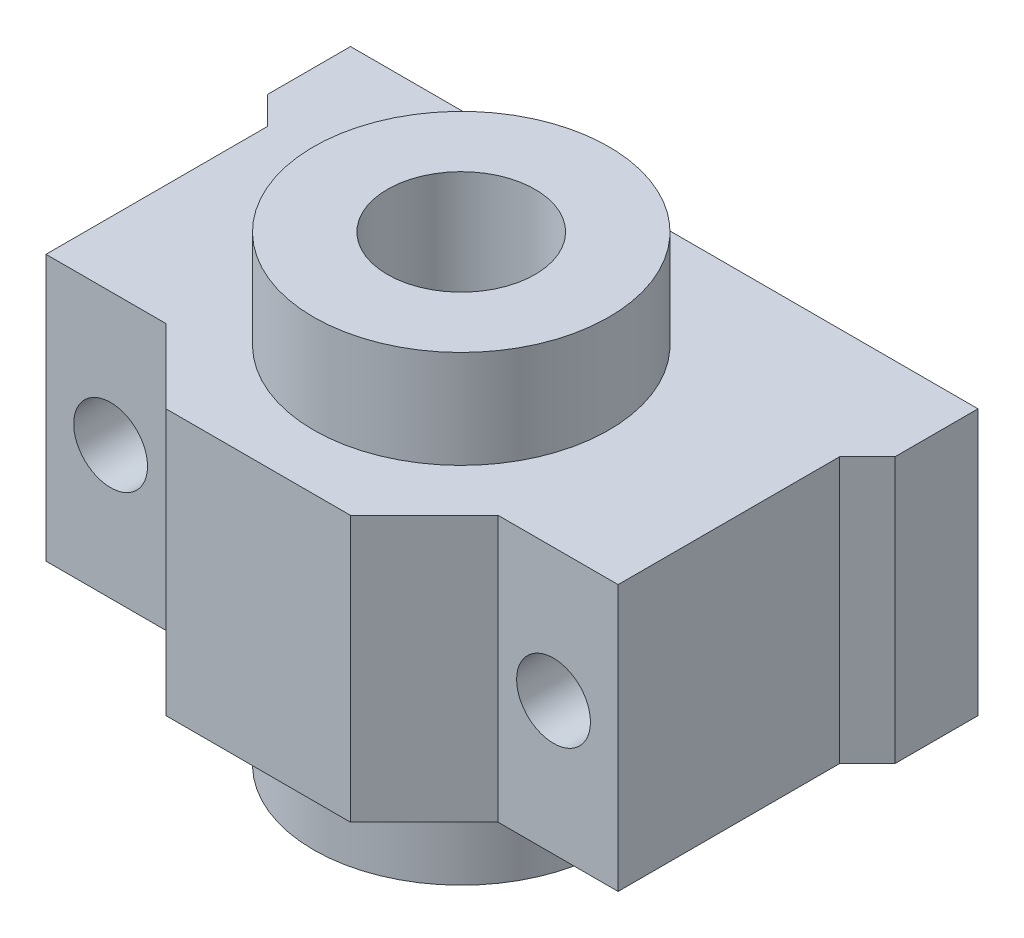
SolidWorks part; units mm, degrees
ref_plane "前视基准面" through (0, 0, 0) normal (0, 0, 1) x (1, 0, 0)
ref_plane "上视基准面" through (0, 0, 0) normal (0, 1, 0) x (1, 0, 0)
ref_plane "右视基准面" through (0, 0, 0) normal (1, 0, 0) x (0, 0, -1)
sketch "草图1" plane through (0, 0, 0) normal (0, 1, 0) x (1, 0, 0)
  circle A0 centre (-68.4706, 17.4118) radius 4
  circle A1 centre (-68.4706, 17.4118) radius 8
  dimension "D1" = 8
  dimension "D2" = 16
extrude "凸台-拉伸1" add sketch "草图1" along normal mid plane 25
sketch "草图2" plane through (0, 0, 0) normal (0, 1, 0) x (1, 0, 0)
  line L1 (-85.4706, 28.4118) -> (-51.4706, 28.4118)
  line L2 (-85.4706, 28.4118) -> (-85.4706, 6.4118)
  line L3 (-85.4706, 6.4118) -> (-51.4706, 6.4118)
  line L4 (-51.4706, 28.4118) -> (-51.4706, 6.4118)
  line L5 (-68.4706, 6.4118) -> (-68.4706, 28.4118) construction
  line L6 (-85.4706, 17.4118) -> (-51.4706, 17.4118) construction
  circle A0 centre (-68.4706, 17.4118) radius 8 construction
  circle A1 centre (-68.4706, 17.4118) radius 8
  dimension "D1" = 34
  dimension "D2" = 22
extrude "凸台-拉伸2" add sketch "草图2" along normal mid plane 14.4
sketch "草图3" plane through (0, 0, 0) normal (0, 1, 0) x (1, 0, 0)
  line L0 (-68.4706, 17.4118) -> (-18.2051, 17.4118) construction
  line L1 (-68.4706, 17.4118) -> (-68.4706, 24.3313) construction
  line L2 (-52.9706, 10.4118) -> (-59.4706, 10.4118)
  line L3 (-85.4706, 23.9118) -> (-83.9706, 22.4118)
  line L4 (-83.9706, 22.4118) -> (-83.9706, 10.4118)
  line L5 (-83.9706, 10.4118) -> (-77.4706, 10.4118)
  line L6 (-51.4706, 6.4118) -> (-51.4706, 28.4118)
  line L7 (-51.4706, 28.4118) -> (-85.4706, 28.4118)
  line L8 (-85.4706, 28.4118) -> (-85.4706, 6.4118)
  line L9 (-85.4706, 6.4118) -> (-51.4706, 6.4118)
  line L10 (-51.4706, 6.4118) -> (-51.4706, 28.4118)
  line L11 (-51.4706, 28.4118) -> (-85.4706, 28.4118)
  line L12 (-85.4706, 28.4118) -> (-85.4706, 6.4118)
  line L13 (-85.4706, 6.4118) -> (-51.4706, 6.4118)
  line L14 (-77.4706, 10.4118) -> (-73.4706, 6.4118)
  line L15 (-59.4706, 10.4118) -> (-63.4706, 6.4118)
  line L16 (-52.9706, 22.4118) -> (-52.9706, 10.4118)
  line L17 (-51.4706, 23.9118) -> (-52.9706, 22.4118)
  line L18 (-85.4706, 23.9118) -> (-85.4706, 28.4118)
  line L19 (-51.4706, 28.4118) -> (-51.4706, 23.9118)
  line L20 (-63.4706, 6.4118) -> (-73.4706, 6.4118)
  circle A0 centre (-68.4706, 17.4118) radius 8 construction
  circle A1 centre (-68.4706, 17.4118) radius 8
  dimension "D2" = 11
  dimension "D3" = 17
  dimension "D4" = 6
  dimension "D5" = 18
  dimension "D6" = 1.5
  dimension "D7" = 45
  dimension "D8" = 5
  dimension "D9" = 45
  dimension "D1" = 0
extrude "切除-拉伸1" cut sketch "草图3" against normal through all both and the other way through all contours L10 L17 L16 L2 L15 L13 | L14 L5 L4 L3 L12 L13
sketch "草图4" plane through (0, 0, 0) normal (0, 0, 1) x (1, 0, 0)
  line L0 (-68.4706, 12.5) -> (-68.4706, -6.9234) construction
  line L2 (-46.9865, 0) -> (-86.9533, 0) construction
  line L3 (-60.4706, 7.2) -> (-60.4706, 12.5)
  line L4 (-60.4706, 7.2) -> (-60.4706, 12.5) construction
  line L5 (-60.4706, 12.5) -> (-76.4706, 12.5)
  line L6 (-85.4706, -7.2) -> (-51.4706, -7.2)
  line L7 (-85.4706, 7.2) -> (-85.4706, -7.2)
  line L8 (-51.4706, 7.2) -> (-85.4706, 7.2)
  line L9 (-51.4706, -7.2) -> (-51.4706, 7.2)
  line L10 (-85.4706, -7.2) -> (-76.4706, -7.2)
  line L11 (-85.4706, 7.2) -> (-85.4706, -7.2)
  line L12 (-51.4706, 7.2) -> (-60.4706, 7.2)
  line L13 (-51.4706, -7.2) -> (-51.4706, 7.2)
  line L14 (-76.4706, 12.5) -> (-76.4706, 7.2)
  line L15 (-76.4706, 12.5) -> (-76.4706, 7.2) construction
  line L16 (-76.4706, -7.2) -> (-76.4706, -12.5)
  line L17 (-76.4706, -7.2) -> (-76.4706, -12.5) construction
  line L18 (-76.4706, -12.5) -> (-60.4706, -12.5)
  line L19 (-60.4706, -12.5) -> (-60.4706, -7.2)
  line L20 (-60.4706, -12.5) -> (-60.4706, -7.2) construction
  line L21 (-76.4706, 7.2) -> (-85.4706, 7.2)
  line L22 (-60.4706, -7.2) -> (-51.4706, -7.2)
  circle A0 centre (-56.4706, 0) radius 2
  circle A1 centre (-80.4706, 0) radius 2
  dimension "D1" = 4
  dimension "D3" = 17
  dimension "D4" = 7.2
  dimension "D5" = 12
  dimension "D2" = 0
extrude "切除-拉伸2" cut sketch "草图4" along normal through all both and the other way through all flip side to cut
